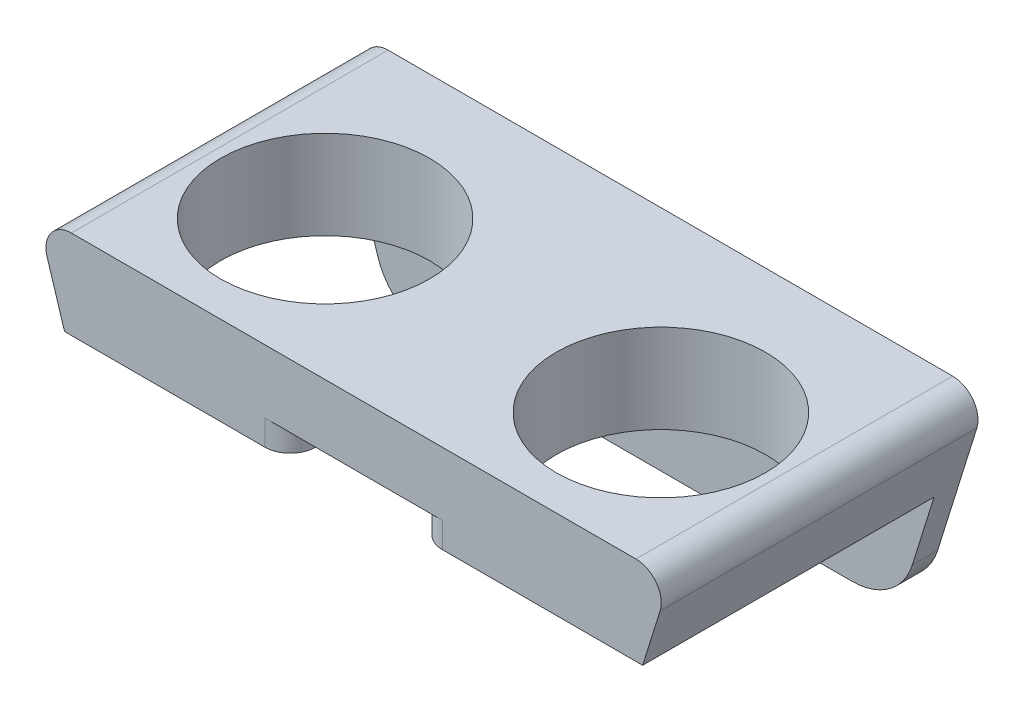
SolidWorks part; units mm, degrees
ref_plane "Front Plane" through (0, 0, 0) normal (0, 0, 1) x (1, 0, 0)
ref_plane "Top Plane" through (0, 0, 0) normal (0, 1, 0) x (1, 0, 0)
ref_plane "Right Plane" through (0, 0, 0) normal (1, 0, 0) x (0, 0, -1)
sketch "Sketch1" plane through (0, 0, 0) normal (0, 1, 0) x (1, 0, 0)
  line L0 (-50, 12) -> (0, 12) construction
  line L1 (-50, 24) -> (0, 24)
  line L2 (-50, 24) -> (-50, 0)
  line L3 (-50, 0) -> (0, 0)
  line L4 (0, 24) -> (0, 0)
  circle A0 centre (-38.25, 12) radius 8.25
  circle A1 centre (-11.75, 12) radius 8.25
  dimension "D3" = 16.5
  dimension "D4" = 16.5
  dimension "D5" = 26.5
  dimension "D1" = 50
  dimension "D2" = 24
  dimension "D6" = 11.75
extrude "Boss-Extrude1" add sketch "Sketch1" along normal blind 7
sketch "Sketch2" plane through (0, 0, 0) normal (0, -1, 0) x (1, 0, 0)
  line L1 (-31.25, -22) -> (-18.75, -22)
  line L2 (-31.25, -22) -> (-31.25, -17.5)
  line L3 (-31.25, -17.5) -> (-18.75, -17.5)
  line L4 (-18.75, -22) -> (-18.75, -17.5)
  line L5 (-25, 0) -> (-25, -24) construction
  line L6 (-50, 0) -> (0, 0) construction
  line L7 (0, -24) -> (-50, -24) construction
  point P14 (-25, -22)
  dimension "D1" = 12.5
  dimension "D2" = 4.5
  dimension "D3" = 2
extrude "Cut-Extrude1" cut sketch "Sketch2" against normal blind 4.0225
sketch "Sketch3" plane through (0, 0, -24) normal (0, 0, -1) x (-1, 0, 0)
  line L0 (50, 7) -> (50, 0) construction
  line L1 (0, 7) -> (50, 7)
  line L2 (0, 7) -> (0, -9)
  line L3 (0, -9) -> (50, -9)
  line L4 (50, 7) -> (50, -9)
  circle A0 centre (12.5, -6) radius 1.55
  circle A1 centre (37.5, -6) radius 1.55
  dimension "D2" = 3.1
  dimension "D3" = 3.1
  dimension "D1" = 16
  dimension "D4" = 25
  dimension "D5" = 12.5
  dimension "D6" = 3
extrude "Boss-Extrude2" add sketch "Sketch3" along normal blind 2
sketch "Sketch4" plane through (0, 0, -24) normal (0, 0, 1) x (1, 0, 0)
  line L0 (-50, 7) -> (-45, -9)
  line L1 (0, -9) -> (-50, -9) construction
  line L2 (-45, -9) -> (-50, -9)
  line L3 (-50, -9) -> (-50, 7)
  line L4 (0, 7) -> (0, -9)
  line L5 (0, -9) -> (-5, -9)
  line L6 (-5, -9) -> (0, 7)
  dimension "D1" = 5
  dimension "D2" = 5
extrude "Cut-Extrude2" cut sketch "Sketch4" against normal through all both and the other way through all
fillet "Fillet1" radius 5 2 edges at (-5, -9, -25) (-45, -9, -25)
fillet "Fillet2" radius 2 2 edges at (-50, 7, -13) (0, 7, -13)
sketch "Sketch5" plane through (0, 0, 0) normal (0, 0, 1) x (1, 0, 0)
  line L1 (-53.5393, 12.092) -> (3.5733, 12.092)
  line L2 (-53.5393, 12.092) -> (-53.5393, -11.0655)
  line L3 (-53.5393, -11.0655) -> (3.5733, -11.0655)
  line L4 (3.5733, 12.092) -> (3.5733, -11.0655)
extrude "Cut-Extrude3" cut sketch "Sketch5" against normal blind 1
sketch "Sketch6" plane through (0, 0, 0) normal (0, -1, 0) x (1, 0, 0)
  line L0 (-47.8125, -1) -> (-2.1875, -1) construction
  line L1 (-30, -1) -> (-20, -1)
  line L2 (-30, -1) -> (-30, -5)
  line L3 (-30, -5) -> (-20, -5)
  line L4 (-20, -1) -> (-20, -5)
  line L5 (-25, -17.5) -> (-25, 6.8179) construction
  line L6 (-18.75, -17.5) -> (-31.25, -17.5) construction
  point P10 (-25, -5)
  dimension "D1" = 10
  dimension "D2" = 4
extrude "Cut-Extrude4" cut sketch "Sketch6" against normal blind 2
fillet "Fillet3" radius 1 2 edges at (-20, 1, -5) (-30, 1, -5)
fillet "Fillet4" radius 2 2 edges at (-20, 1, -1) (-30, 1, -1)
